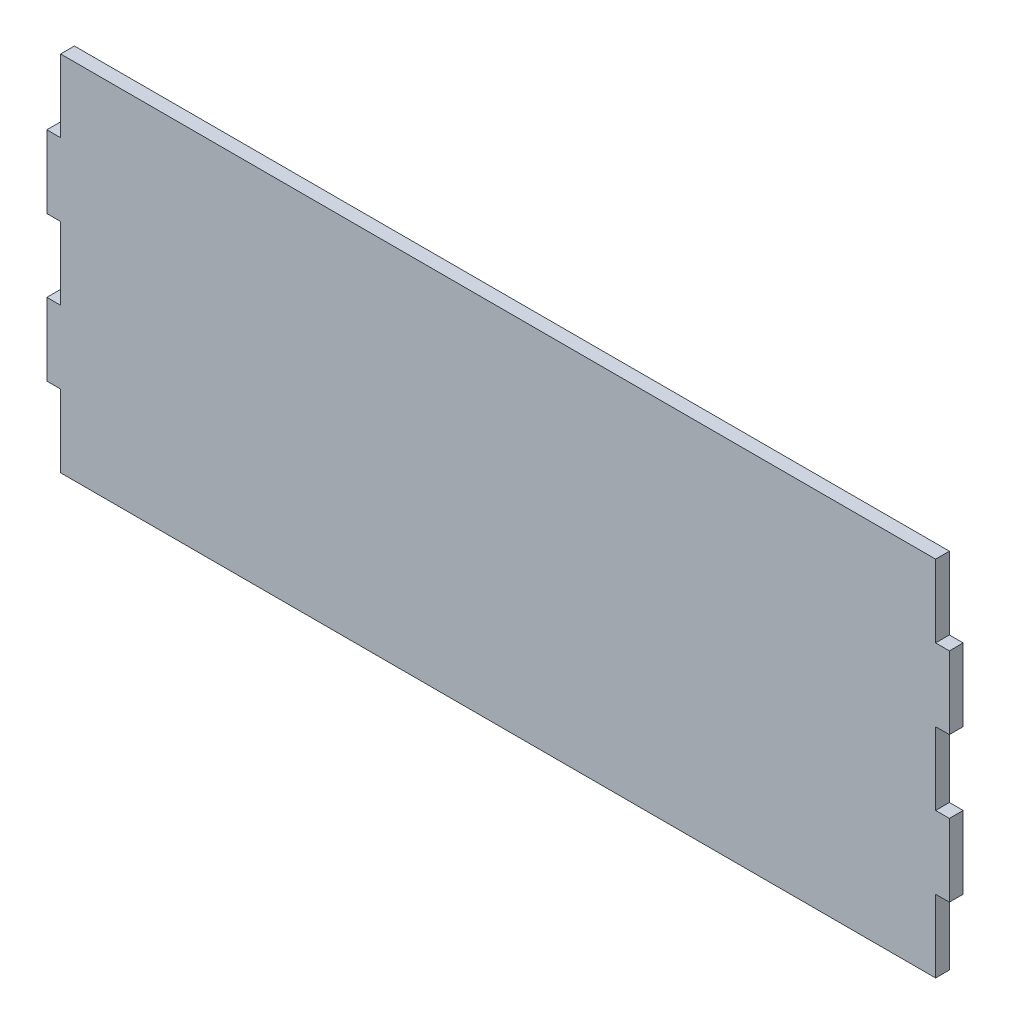
SolidWorks part; units mm, degrees
material "1060 Alloy"
ref_plane "Front Plane" through (0, 0, 0) normal (0, 0, 1) x (1, 0, 0)
ref_plane "Top Plane" through (0, 0, 0) normal (0, 1, 0) x (1, 0, 0)
ref_plane "Right Plane" through (0, 0, 0) normal (1, 0, 0) x (0, 0, -1)
sketch "Sketch2" plane through (0, 0, 0) normal (0, 0, 1) x (1, 0, 0)
  line L0 (311.15, 127) -> (311.15, 101.6) construction
  line L1 (0, 0) -> (622.3, 0) construction
  line L2 (0, 0) -> (0, 127) construction
  line L3 (0, 127) -> (622.3, 127) construction
  line L4 (622.3, 0) -> (622.3, 127) construction
  line L5 (4.826, 76.2) -> (4.826, 50.8)
  line L6 (4.826, 127) -> (311.15, 127)
  line L7 (4.826, 127) -> (4.826, 101.6)
  line L8 (4.826, 0) -> (311.15, 0)
  line L9 (311.15, 127) -> (311.15, 101.6)
  line L10 (0, 101.6) -> (4.826, 101.6)
  line L11 (0, 101.6) -> (0, 76.2)
  line L12 (0, 76.2) -> (4.826, 76.2)
  line L13 (311.15, 76.2) -> (311.15, 50.8) construction
  line L14 (4.826, 50.8) -> (0, 50.8)
  line L15 (311.15, 25.4) -> (311.15, 0) construction
  line L16 (4.826, 25.4) -> (0, 25.4)
  line L17 (0, 50.8) -> (0, 25.4)
  line L18 (4.826, 25.4) -> (4.826, 0)
  line L19 (311.15, 101.6) -> (315.976, 101.6)
  line L21 (311.15, 76.2) -> (315.976, 76.2)
  line L22 (315.976, 101.6) -> (315.976, 76.2)
  line L23 (311.15, 50.8) -> (315.976, 50.8)
  line L25 (311.15, 25.4) -> (315.976, 25.4)
  line L26 (315.976, 50.8) -> (315.976, 25.4)
  line L27 (311.15, 76.2) -> (311.15, 50.8)
  line L28 (311.15, 25.4) -> (311.15, 0)
  dimension "D1" = 622.3
  dimension "D2" = 127
  dimension "D3" = 4.826
  dimension "D4" = 4.826
extrude "Boss-Extrude1" add sketch "Sketch2" along normal blind 4.826
equation "\"sheet width\"= .19"
equation "\"width\"= 24.5"
equation "\"length\"= 34.5"
equation "\"standoff hole size\"= .5"
equation "\"ground clearence\"= 3"
equation "\"small drive pulley\"= 74.55mm"
equation "\"large drive pulley\"= 150.95mm"
equation "\"drive axle hole size\"= .5"
equation "\"front pulley clearence\"= 1"
equation "\"center support location\"= 19"
equation "\"inner to outer wall size\"= 3.75"
equation "\"D1@Sketch2\"=\"width\""
equation "\"D3@Sketch2\"=\"sheet width\""
equation "\"D4@Sketch2\"=\"sheet width\""
equation "\"D1@Boss-Extrude1\"=\"sheet width\""
